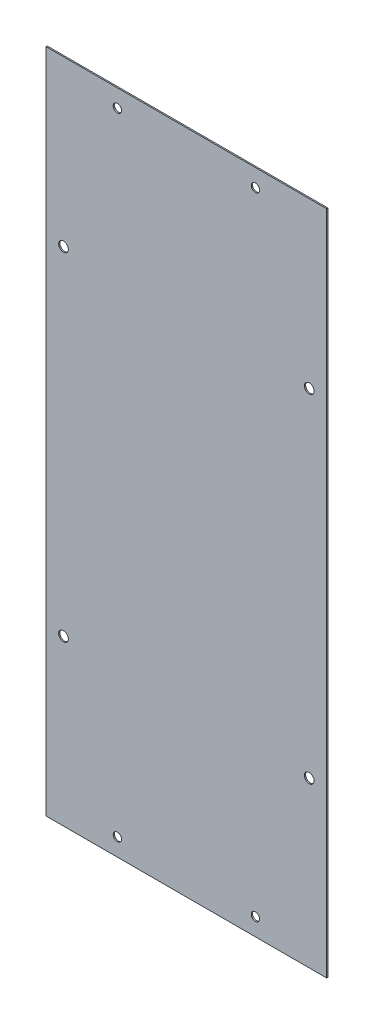
SolidWorks part; units mm, degrees
ref_plane "前视基准面" through (0, 0, 0) normal (0, 0, 1) x (1, 0, 0)
ref_plane "上视基准面" through (0, 0, 0) normal (0, 1, 0) x (1, 0, 0)
ref_plane "右视基准面" through (0, 0, 0) normal (1, 0, 0) x (0, 0, -1)
sketch "草图1" plane through (0, 0, 0) normal (0, 0, 1) x (1, 0, 0)
  line L1 (-101.6, 241.3) -> (101.6, 241.3)
  line L2 (-101.6, 241.3) -> (-101.6, -241.3)
  line L3 (-101.6, -241.3) -> (101.6, -241.3)
  line L4 (101.6, 241.3) -> (101.6, -241.3)
  line L5 (-101.6, 241.3) -> (101.6, -241.3) construction
  line L6 (-101.6, -241.3) -> (101.6, 241.3) construction
  point P0 (0, 0)
  dimension "D1" = 203.2
  dimension "D2" = 482.6
extrude "凸台-拉伸1" add sketch "草图1" along normal blind 0.9
sketch "草图2" plane through (0, 0, 0.9) normal (0, 0, 1) x (1, 0, 0)
  line L2 (-89, 122.2) -> (89, 122.2) construction
  line L5 (-89, 122.2) -> (-89, -122.2) construction
  line L6 (0, 0) -> (50, 0) construction
  line L7 (0, 0) -> (0, 51.14) construction
  line L8 (0, 0) -> (0, 228.6) construction
  line L9 (0, 228.6) -> (50, 228.6) construction
  circle A0 centre (-89, 122.2) radius 3.5
  circle A1 centre (89, 122.2) radius 3.5
  circle A2 centre (89, -122.2) radius 3.5
  circle A3 centre (-89, -122.2) radius 3.5
  circle A4 centre (50, 228.6) radius 3
  circle A5 centre (50, -228.6) radius 3
  circle A6 centre (-50, 228.6) radius 3
  circle A7 centre (-50, -228.6) radius 3
  dimension "D1" = 122.2
  dimension "D2" = 228.6
  dimension "D4" = 50
  dimension "D3" = 178
extrude "切除-拉伸1" cut sketch "草图2" against normal blind 10
